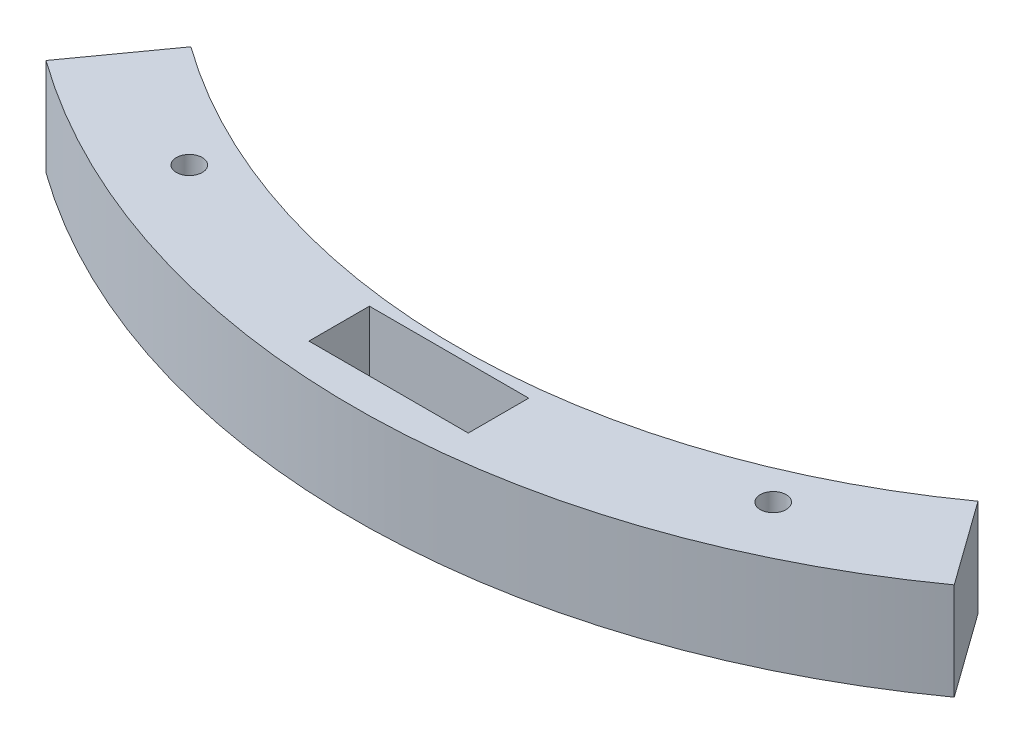
SolidWorks part; units mm, degrees
ref_plane "Alzado" through (0, 0, 0) normal (0, 0, 1) x (1, 0, 0)
ref_plane "Planta" through (0, 0, 0) normal (0, 1, 0) x (1, 0, 0)
ref_plane "Vista lateral" through (0, 0, 0) normal (1, 0, 0) x (0, 0, -1)
sketch "Croquis1" plane through (0, 0, 0) normal (0, 1, 0) x (1, 0, 0)
  line L0 (35, -48.734) -> (30.3333, -42.2361)
  line L1 (-35, -48.734) -> (-30.3333, -42.2361)
  line L8 (-5.14, -55) -> (5.14, -55) construction
  line L9 (0, 0) -> (-22.5, -50.1871) construction
  line L10 (-22.5, -50.1871) -> (22.5, -50.1871) construction
  line L16 (22.5, -50.1871) -> (0, 0) construction
  line L17 (-5.14, -56.33) -> (-5.14, -53.67)
  line L18 (-5.14, -53.67) -> (5.14, -53.67)
  line L19 (5.14, -56.33) -> (5.14, -53.67)
  line L20 (-5.14, -56.33) -> (5.14, -56.33)
  arc A0 (-35, -48.734) -> (35, -48.734) centre (0, 0) ccw
  arc A1 (-30.3333, -42.2361) -> (30.3333, -42.2361) centre (0, 0) ccw
  arc A12 (-22.5, -50.1871) -> (22.5, -50.1871) centre (0, 0) ccw construction
  circle A13 centre (-22.5, -50.1871) radius 1
  circle A14 centre (22.5, -50.1871) radius 1
  dimension "D1" = 120
  dimension "D15" = 55
  dimension "D17" = 2
  dimension "D2" = 70
  dimension "D3" = 8
  dimension "D13" = 10.28
  dimension "D14" = 2.66
  dimension "45" = 45
extrude "Saliente-Extruir1" add sketch "Croquis1" along normal blind 7.5
sketch "Croquis2" plane through (0, 7.5, 0) normal (0, 1, 0) x (1, 0, 0)
  line L0 (5.14, -53.67) -> (-5.14, -53.67) construction
  line L1 (5.14, -56.33) -> (5.14, -53.67) construction
  line L2 (-5.14, -56.33) -> (5.14, -56.33) construction
  line L3 (-5.14, -53.67) -> (-5.14, -56.33) construction
  line L4 (5.14, -53.67) -> (-5.14, -53.67) construction
  line L5 (5.14, -56.33) -> (5.14, -53.67) construction
  line L6 (-5.14, -56.33) -> (5.14, -56.33) construction
  line L7 (-5.14, -53.67) -> (-5.14, -56.33) construction
  line L8 (6.14, -52.67) -> (-6.14, -52.67)
  line L9 (-6.14, -52.67) -> (-6.14, -57.33)
  line L10 (-6.14, -57.33) -> (6.14, -57.33)
  line L11 (6.14, -57.33) -> (6.14, -52.67)
  dimension "D1" = 1
extrude "Cortar-Extruir1" cut sketch "Croquis2" against normal offset from surface (5.5 mm away) 2 up to face at (0, 0, 50.7425)
